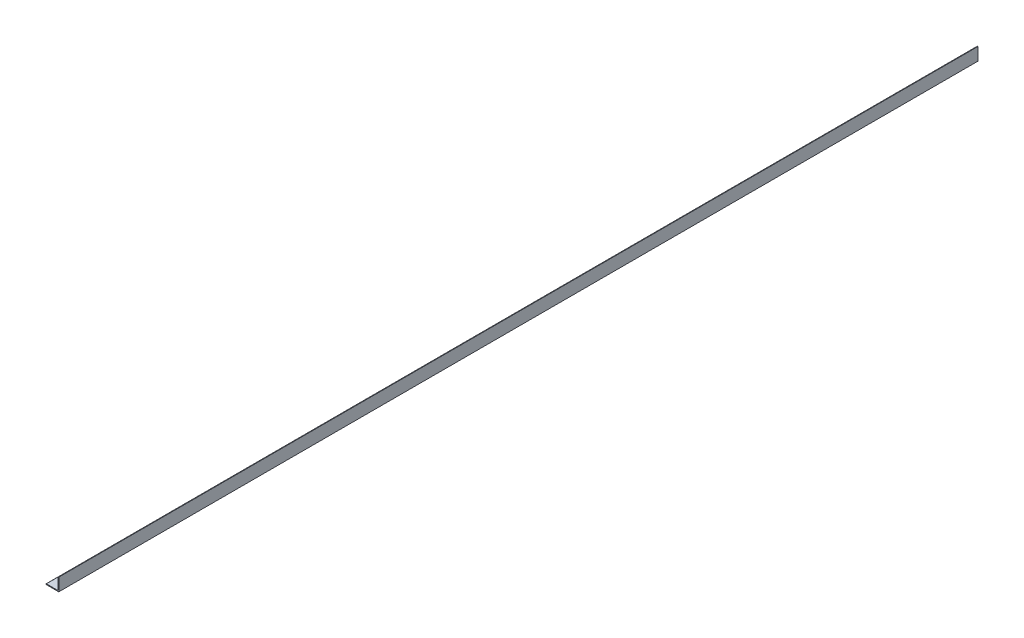
SolidWorks part; units mm, degrees
ref_plane "Front Plane" through (0, 0, 0) normal (0, 0, 1) x (1, 0, 0)
ref_plane "Top Plane" through (0, 0, 0) normal (0, 1, 0) x (1, 0, 0)
ref_plane "Right Plane" through (0, 0, 0) normal (1, 0, 0) x (0, 0, -1)
sketch "Sketch0" plane through (0, 0, 0) normal (0, 0, 1) x (1, 0, 0)
  line L0 (-12.7, -12.7) -> (12.7, -12.7)
  line L1 (12.7, -12.7) -> (12.7, 12.7)
  line L2 (12.7, 0) -> (0, 0) construction
  line L3 (0, 0) -> (0, -12.7) construction
  line L4 (11.1125, -9.5377) -> (11.1125, 12.7) construction
  line L5 (9.5377, -11.1125) -> (-12.7, -11.1125) construction
  arc A0 (11.1125, -9.5377) -> (9.5377, -11.1125) centre (9.5377, -9.5377) cw
  point P3 (10.6513, -10.6513)
  dimension "Inside Corner Radius" = 1.5748
  dimension "Outside Height" = 25.4
  dimension "Inside Height" = 23.8125
  dimension "Inside Width" = 23.8125
  dimension "Wall Thickness" = 1.5875
  dimension "D1" = 1.5875
  dimension "Outside Width" = 25.4
sketch "Sketch1" plane through (0, 0, 0) normal (1, 0, 0) x (0, 0, -1)
  line L0 (914.4, 0) -> (-914.4, 0)
  point P4 (0, 0)
  dimension "Length" = 1828.8
sketch "Sketch2" plane through (0, 0, 0) normal (0, 0, 1) x (1, 0, 0)
  line L0 (-12.7, -12.7) -> (12.7, -12.7)
  line L1 (12.7, -12.7) -> (12.7, 12.7)
  line L2 (12.7, 12.7) -> (11.1125, 12.7) construction
  line L3 (11.1125, 11.9062) -> (11.1125, -9.5377)
  line L4 (9.5377, -11.1125) -> (-11.9062, -11.1125)
  line L5 (-12.7, -12.7) -> (-12.7, -11.1125) construction
  line L6 (11.9062, 12.7) -> (12.7, 12.7)
  line L7 (-12.7, -11.9062) -> (-12.7, -12.7)
  line L8 (12.7, 0) -> (0, 0) construction
  line L9 (0, 0) -> (0, -12.7) construction
  arc A0 (11.1125, 11.9062) -> (11.9062, 12.7) centre (11.9062, 11.9062) cw
  arc A1 (-12.7, -11.9062) -> (-11.9062, -11.1125) centre (-11.9062, -11.9062) cw
  arc A2 (11.1125, -9.5377) -> (9.5377, -11.1125) centre (9.5377, -9.5377) cw
  dimension "Inside Radius" = 1.5748
  dimension "Height" = 25.4
  dimension "Width" = 25.4
  dimension "Thickness" = 1.5875
extrude "Boss-Extrude1" add sketch "Sketch2" along normal mid plane 1828.8
sketch "Break Locations" plane through (0, 0, 0) normal (1, 0, 0) x (0, 0, -1)
  line L0 (-888.492, 0) -> (888.492, 0)
  line L1 (-914.4, -12.7) -> (-914.4, 12.7) construction
  line L2 (914.4, -12.7) -> (914.4, 12.7) construction
  point P0 (-892.81, 0)
  point P1 (892.81, 0)
  point P10 (0, 0)
  point P11 (888.492, 0)
  point P13 (-888.492, 0)
  dimension "D1" = 21.59
  dimension "D2" = 21.59
  dimension "D3" = 25.908
hole_wizard "1/4-20 Tapped Hole1" positions "Sketch3" profile "Sketch4" tap size "1/4-20" standard "ANSI Inch" end condition through all
sketch "Sketch3" plane through (0, -11.1125, 0) normal (0, 1, 0) x (1, 0, 0)
  line L2 (11.1125, -914.4) -> (11.1125, 914.4) construction
  line L3 (9.5377, -914.4) -> (-11.9062, -914.4) construction
  point P0 (-1.5875, -661.924)
  point P3 (-1.5875, -661.924)
  point P11 (-1.5875, -206.248)
  point P13 (-1.5875, 705.104)
  point P15 (-1.5875, 249.428)
  dimension "D1" = 12.7
  dimension "D2" = 252.476
  dimension "D3" = 455.676
  dimension "D4" = 455.676
  dimension "D5" = 455.676
cosmetic thread "Hole Thread1" parameters "D2"=6.35
sketch "Sketch4" plane through (-1.5875, -11.1125, 661.924) normal (1, 0, 0) x (0, 0, 1)
  line L0 (0, 0) -> (0, 1.5875)
  line L1 (0, 1.5875) -> (2.5527, 1.5875)
  line L2 (2.5527, 1.5875) -> (2.5527, 0)
  line L5 (2.5527, 0) -> (0, 0)
  line L11 (0, -6.35) -> (0, 107.95) construction
  dimension "Thru Tap Drill Dia." = 5.1054
  dimension "Thru Tap Drill Depth" = 1.5875
cosmetic thread "Hole Thread2" parameters "D2"=6.35
cosmetic thread "Hole Thread3" parameters "D2"=6.35
cosmetic thread "Hole Thread4" parameters "D2"=6.35
sketch "Sketch5" plane through (0, -11.1125, 0) normal (0, 1, 0) x (1, 0, 0)
  line L0 (-1.5875, -701.675) -> (-1.5875, -720.725) construction
  line L1 (1.4605, -701.675) -> (1.4605, -720.725)
  line L2 (-4.6355, -701.675) -> (-4.6355, -720.725)
  line L3 (9.5377, -914.4) -> (-11.9062, -914.4) construction
  line L4 (11.1125, -914.4) -> (11.1125, 914.4) construction
  line L5 (-1.5875, -285.75) -> (-1.5875, -304.8) construction
  line L6 (1.4605, -285.75) -> (1.4605, -304.8)
  line L7 (-4.6355, -285.75) -> (-4.6355, -304.8)
  line L8 (-57.0785, 0) -> (40.0941, 0) construction
  line L9 (-1.5875, 317.5) -> (-1.5875, 336.55) construction
  line L10 (1.4605, 317.5) -> (1.4605, 336.55)
  line L11 (-4.6355, 317.5) -> (-4.6355, 336.55)
  line L12 (-1.5875, 717.55) -> (-1.5875, 736.6) construction
  line L13 (1.4605, 717.55) -> (1.4605, 736.6)
  line L14 (-4.6355, 717.55) -> (-4.6355, 736.6)
  line L15 (9.5377, 914.4) -> (-11.9062, 914.4) construction
  arc A0 (1.4605, -701.675) -> (-4.6355, -701.675) centre (-1.5875, -701.675) ccw
  arc A1 (-4.6355, -720.725) -> (1.4605, -720.725) centre (-1.5875, -720.725) ccw
  arc A2 (1.4605, -285.75) -> (-4.6355, -285.75) centre (-1.5875, -285.75) ccw
  arc A3 (-4.6355, -304.8) -> (1.4605, -304.8) centre (-1.5875, -304.8) ccw
  arc A4 (1.4605, 317.5) -> (-4.6355, 317.5) centre (-1.5875, 317.5) cw
  arc A5 (-4.6355, 336.55) -> (1.4605, 336.55) centre (-1.5875, 336.55) cw
  arc A6 (1.4605, 717.55) -> (-4.6355, 717.55) centre (-1.5875, 717.55) cw
  arc A7 (-4.6355, 736.6) -> (1.4605, 736.6) centre (-1.5875, 736.6) cw
  point P2 (-1.5875, -711.2)
  point P13 (-1.5875, -295.275)
  point P23 (-1.5875, 327.025)
  point P30 (-1.5875, 727.075)
  dimension "D2" = 3.048
  dimension "D5" = 3.048
  dimension "D12" = 3.048
  dimension "D13" = 3.048
  dimension "D1" = 19.05
  dimension "D3" = 203.2
  dimension "D4" = 12.7
  dimension "D6" = 19.05
  dimension "D7" = 609.6
  dimension "D8" = 317.5
  dimension "D9" = 177.8
  dimension "D10" = 12.7
  dimension "D11" = 12.7
extrude "Cut-Extrude1" cut sketch "Sketch5" against normal through all
equation "\"D1@Break Locations\" = .85 * \"Height@Sketch2\""
equation "\"D2@Break Locations\"=\"D1@Break Locations\""
equation "\"Thickness@Sketch2\"=\"wall thickness@sketch0\""
equation "\"Height@Sketch2\"=\"outside height@sketch0\""
equation "\"Width@Sketch2\"=\"outside width@sketch0\""
equation "\"Inside Radius@Sketch2\"=\"inside corner radius@sketch0\""
equation "\"Length@Boss-Extrude1\"=\"length@sketch1\""
equation "\"D3@Break Locations\"=\"D2@Break Locations\"*1.2"
equation "\"D1@Sketch0\"=\"Wall Thickness@Sketch0\""
